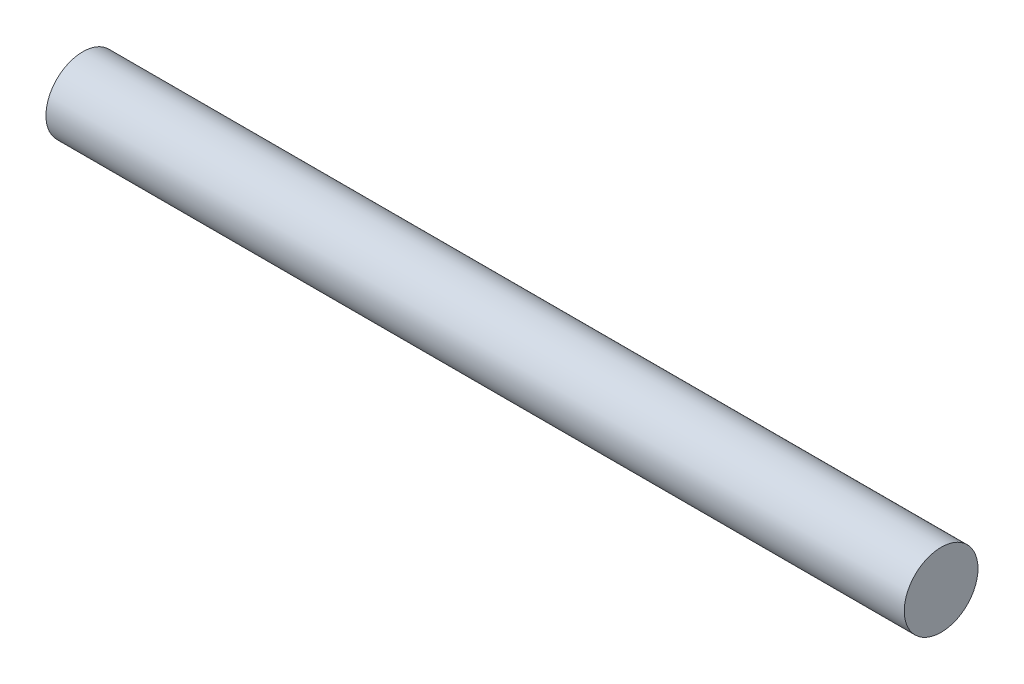
SolidWorks part; units mm, degrees
ref_plane "Front Plane" through (0, 0, 0) normal (0, 0, 1) x (1, 0, 0)
ref_plane "Top Plane" through (0, 0, 0) normal (0, 1, 0) x (1, 0, 0)
ref_plane "Right Plane" through (0, 0, 0) normal (1, 0, 0) x (0, 0, -1)
sketch "Sketch1" plane through (0, 0, 0) normal (1, 0, 0) x (0, 0, -1)
  circle A0 centre (0, 0) radius 2.75
  dimension "D1" = 5.5
extrude "Boss-Extrude1" add sketch "Sketch1" along normal mid plane 64
